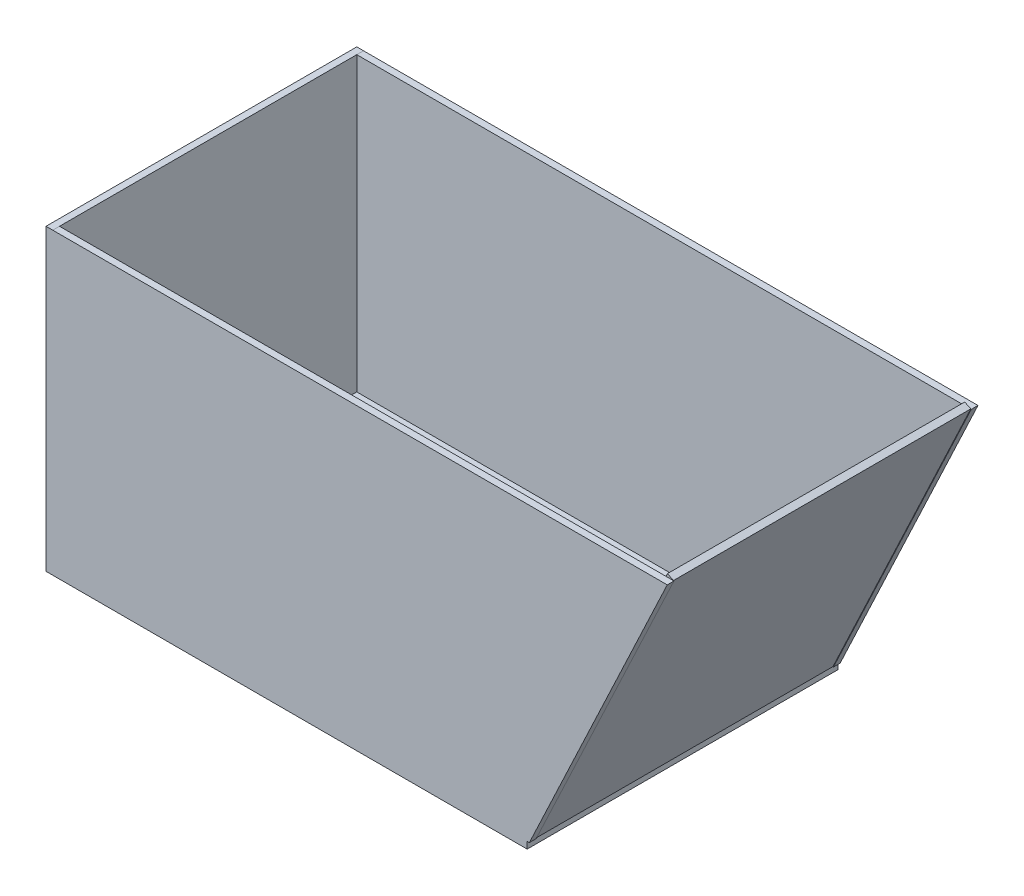
SolidWorks part; units mm, degrees
material "Oak"
ref_plane "Front Plane" through (0, 0, 0) normal (0, 0, 1) x (1, 0, 0)
ref_plane "Top Plane" through (0, 0, 0) normal (0, 1, 0) x (1, 0, 0)
ref_plane "Right Plane" through (0, 0, 0) normal (1, 0, 0) x (0, 0, -1)
sketch "Sketch1" plane through (0, 0, 0) normal (0, 1, 0) x (1, 0, 0)
  line L1 (-226.5, -146.2848) -> (226.5, -146.2848)
  line L2 (-226.5, -146.2848) -> (-226.5, 146.2848)
  line L3 (-226.5, 146.2848) -> (226.5, 146.2848)
  line L4 (226.5, -146.2848) -> (226.5, 146.2848)
  line L5 (-226.5, -146.2848) -> (226.5, 146.2848) construction
  line L6 (-226.5, 146.2848) -> (226.5, -146.2848) construction
  point P0 (0, 0)
  dimension "D1" = 453
extrude "Boss-Extrude1" add sketch "Sketch1" along normal blind 6.35
sketch "Sketch2" plane through (0, 6.35, 0) normal (0, 1, 0) x (1, 0, 0)
  line L0 (-226.5, -146.2848) -> (226.5, -146.2848) construction
  line L1 (-226.5, 146.2848) -> (-220.15, 146.2848)
  line L2 (-226.5, 146.2848) -> (-226.5, -146.2848)
  line L3 (-226.5, -146.2848) -> (-220.15, -146.2848)
  line L4 (-220.15, 146.2848) -> (-220.15, -146.2848)
  dimension "D1" = 6.35
extrude "Boss-Extrude2" add sketch "Sketch2" along normal blind 275
sketch "Sketch4" plane through (0, 0, 146.2848) normal (0, 0, 1) x (1, 0, 0)
  line L4 (358.3925, 281.4233) -> (228.5702, 6.35)
  line L5 (228.5702, 6.35) -> (-220.15, 6.35)
  line L6 (-220.15, 6.35) -> (-220.15, 281.35)
  line L7 (-220.15, 281.35) -> (358.3925, 281.4233)
  point P4 (0, 0)
  point P6 (0, 0)
  point P7 (0, 0)
extrude "Boss-Extrude3" add sketch "Sketch4" against normal blind 6.35
mirror "Mirror1" about plane through (0, 0, 0) normal (0, 0, 1) of "Boss-Extrude3"
sketch "Sketch5" plane through (184.0656, -86.8707, 0) normal (0.9043, -0.4268, 0) x (0, 0, -1)
  line L9 (-139.9348, 407.4679) -> (139.9348, 407.4679)
  line L10 (-139.9348, 407.4679) -> (-139.9348, 103.2984)
  line L11 (-139.9348, 103.2984) -> (139.9348, 103.2984)
  line L12 (139.9348, 407.4679) -> (139.9348, 103.2984)
extrude "Boss-Extrude5" add sketch "Sketch5" against normal blind 6.35 separate body
